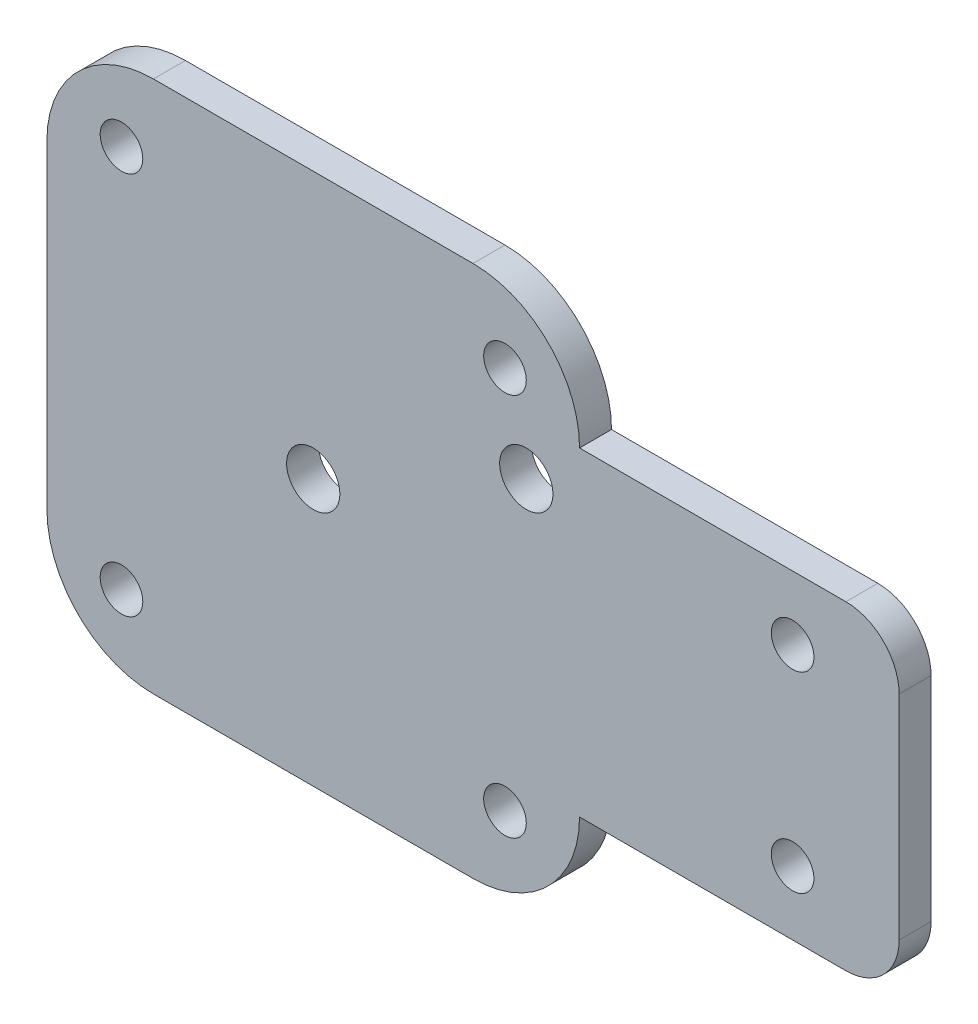
SolidWorks part; units mm, degrees
ref_plane "Alzado" through (0, 0, 0) normal (0, 0, 1) x (1, 0, 0)
ref_plane "Planta" through (0, 0, 0) normal (0, 1, 0) x (1, 0, 0)
ref_plane "Vista lateral" through (0, 0, 0) normal (1, 0, 0) x (0, 0, -1)
sketch "Croquis1" plane through (0, 0, 0) normal (0, 0, 1) x (1, 0, 0)
  line L0 (0, 25) -> (25, 25) construction
  line L1 (10, 0) -> (40, 0)
  line L2 (0, 10) -> (0, 40)
  line L3 (10, 50) -> (40, 50)
  line L4 (50, 10) -> (50, 40)
  line L5 (25, 50) -> (25, 25) construction
  line L6 (70, 34) -> (70, 16) construction
  line L7 (50, 40) -> (75, 40)
  line L8 (50, 40) -> (50, 10)
  line L9 (50, 10) -> (75, 10)
  line L10 (80, 35) -> (80, 15)
  line L11 (7, 43) -> (43, 43) construction
  line L12 (43, 7) -> (43, 43) construction
  line L13 (7, 43) -> (7, 7) construction
  line L14 (7, 7) -> (43, 7) construction
  arc A0 (10, 0) -> (0, 10) centre (10, 10) cw
  arc A1 (40, 0) -> (50, 10) centre (40, 10) ccw
  arc A2 (40, 50) -> (50, 40) centre (40, 40) cw
  arc A3 (0, 40) -> (10, 50) centre (10, 40) cw
  circle A4 centre (7, 43) radius 2
  circle A5 centre (43, 43) radius 2
  circle A6 centre (43, 7) radius 2
  circle A7 centre (7, 7) radius 2
  circle A8 centre (25, 25) radius 2.5
  arc A9 (75, 10) -> (80, 15) centre (75, 15) ccw
  arc A10 (75, 40) -> (80, 35) centre (75, 35) cw
  circle A11 centre (70, 34) radius 2
  circle A12 centre (70, 16) radius 2
  circle A13 centre (45, 35) radius 2.5
  point P7 (0, 0)
  point P12 (50, 50)
  point P15 (0, 50)
  point P34 (80, 40)
  dimension "D3" = 10
  dimension "D4" = 4
  dimension "D8" = 5
  dimension "D9" = 4
  dimension "D10" = 4
  dimension "D12" = 20
  dimension "D14" = 5
  dimension "D17" = 5
  dimension "D1" = 50
  dimension "D2" = 50
  dimension "D5" = 7
  dimension "D6" = 7
  dimension "D7" = 30
  dimension "D11" = 18
  dimension "D13" = 6
  dimension "D15" = 15
  dimension "D16" = 5
extrude "Saliente-Extruir1" add sketch "Croquis1" along normal blind 3 contours A3 L2 A0 L1 A1 L4 A2 L3 A13 A8 A5 A4 A6 A7 | A10 L7 L4 L9 A9 L10 A12 A11
